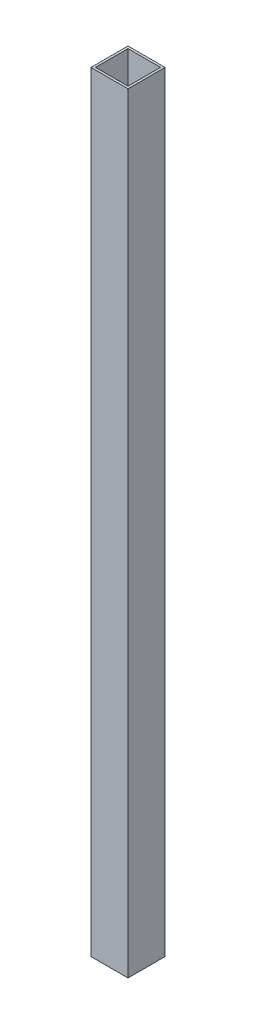
SolidWorks part; units mm, degrees
ref_plane "Front Plane" through (0, 0, 0) normal (0, 0, 1) x (1, 0, 0)
ref_plane "Top Plane" through (0, 0, 0) normal (0, 1, 0) x (1, 0, 0)
ref_plane "Right Plane" through (0, 0, 0) normal (1, 0, 0) x (0, 0, -1)
sketch "Sketch1" plane through (0, 0, 0) normal (0, 1, 0) x (1, 0, 0)
  line L1 (-33.3375, 19.4469) -> (-7.9375, 19.4469)
  line L2 (-33.3375, 19.4469) -> (-33.3375, -5.9531)
  line L3 (-33.3375, -5.9531) -> (-7.9375, -5.9531)
  line L4 (-7.9375, 19.4469) -> (-7.9375, -5.9531)
  line L5 (-31.8135, 17.9229) -> (-9.4615, 17.9229)
  line L6 (-31.8135, 17.9229) -> (-31.8135, -4.4291)
  line L7 (-31.8135, -4.4291) -> (-9.4615, -4.4291)
  line L8 (-9.4615, 17.9229) -> (-9.4615, -4.4291)
  dimension "D1" = 25.4
  dimension "D2" = 25.4
  dimension "D3" = 1.524
  dimension "D4" = 1.524
  dimension "D5" = 1.524
  dimension "D6" = 1.524
extrude "Boss-Extrude1" add sketch "Sketch1" along normal blind 528.32
